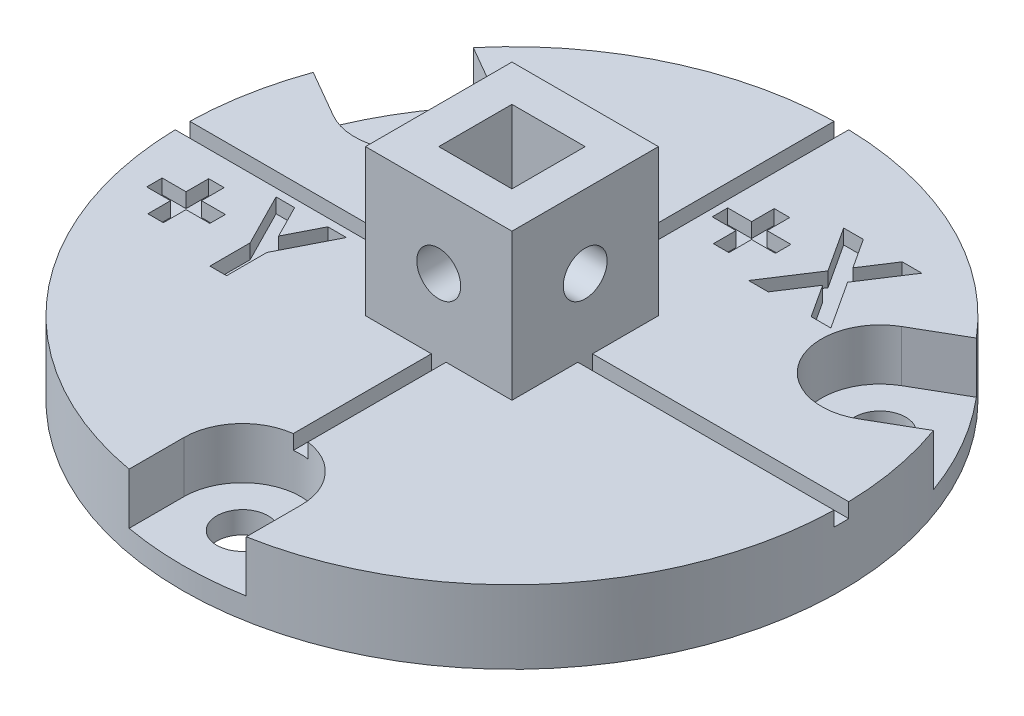
SolidWorks part; units mm, degrees
ref_plane "Front" through (0, 0, 0) normal (0, 0, 1) x (1, 0, 0)
ref_plane "Top" through (0, 0, 0) normal (0, 1, 0) x (1, 0, 0)
ref_plane "Right" through (0, 0, 0) normal (1, 0, 0) x (0, 0, -1)
sketch "Sketch1" plane through (0, 0, 0) normal (0, 1, 0) x (1, 0, 0)
  line L0 (0, 22.5) -> (0, -22.5) construction
  line L1 (22.5, 0) -> (-22.5, 0) construction
  circle A0 centre (0, 0) radius 22.5
  circle A1 centre (0, 0) radius 18.4 construction
  arc A2 (-10.9795, -19.6393) -> (-7.9114, -21.0632) centre (-9.4455, -20.3512) cw construction
  point P19 (0, 0)
  dimension "D1" = 45
  dimension "D2" = 36.8
extrude "plate" add sketch "Sketch1" along normal blind 5
sketch "Sketch6" plane through (0, 5, 0) normal (0, 1, 0) x (1, 0, 0)
  line L0 (0, 22.5) -> (0, -22.5) construction
  line L1 (0, -22.5) -> (0, -18.4) construction
  line L2 (-4, -22.5) -> (-4, -18.4)
  line L3 (4, -22.5) -> (4, -18.4)
  circle A1 centre (0, 0) radius 18.4 construction
  circle A2 centre (0, 0) radius 22.5 construction
  arc A3 (-4, -22.5) -> (4, -22.5) centre (0, -22.5) ccw
  arc A4 (4, -18.4) -> (-4, -18.4) centre (0, -18.4) ccw
  point P7 (0, -20.45)
  dimension "D1" = 4
extrude "opening for screw" cut sketch "Sketch6" against normal blind 5 from offset 1.5 contours L3 A4 L2 A3
sketch "Sketch7" plane through (0, 1.5, 0) normal (0, 1, 0) x (1, 0, 0)
  line L0 (0, 22.5) -> (0, -22.5) construction
  circle A0 centre (0, -18.4) radius 1.75
  circle A1 centre (0, 0) radius 18.4 construction
  dimension "D1" = 3.5
extrude "screw hole" cut sketch "Sketch7" against normal blind 5
pattern_circular "CirPattern20" count 3 over 360 about axis through (0, 0, 0) along (0, 1, 0) of "opening for screw", "screw hole"
sketch "Sketch10" plane through (0, 5, 0) normal (0, 1, 0) x (1, 0, 0)
  line L1 (-22.5, 0.5) -> (22.5, 0.5)
  line L2 (-22.5, 0.5) -> (-22.5, -0.5)
  line L3 (-22.5, -0.5) -> (22.5, -0.5)
  line L4 (22.5, 0.5) -> (22.5, -0.5)
  line L5 (-0.5, 22.5) -> (0.5, 22.5)
  line L6 (-0.5, 22.5) -> (-0.5, -22.5)
  line L7 (-0.5, -22.5) -> (0.5, -22.5)
  line L8 (0.5, 22.5) -> (0.5, -22.5)
  line L9 (0, 22.5) -> (0, -22.5) construction
  point P4 (22.5, 0)
  point P9 (-22.5, 0)
  point P14 (0, -22.5)
  point P15 (0, 22.5)
  dimension "D1" = 1
  dimension "D2" = 1
extrude "Cut-Extrude5" cut sketch "Sketch10" against normal blind 1 contours L6 L7 L8 L5 | L1 L4 L3 L2
sketch "Sketch11" plane through (0, 5, 0) normal (0, 1, 0) x (1, 0, 0)
  line L0 (0.5, 22.4944) -> (0.5, 0.5) construction
  text T0 "<b>+X</b>"
  text T1 "<b>+Y</b>"
extrude "Cut-Extrude6" cut sketch "Sketch11" against normal blind 1
sketch "Sketch12" plane through (0, 5, 0) normal (0, 1, 0) x (1, 0, 0)
  line L0 (0, 5) -> (0, -5) construction
  line L1 (-5, 5) -> (5, 5)
  line L2 (-5, 5) -> (-5, -5)
  line L3 (-5, -5) -> (5, -5)
  line L4 (5, 5) -> (5, -5)
  line L5 (-5, 0) -> (5, 0) construction
  line L9 (-2.5, 2.5) -> (2.5, 2.5)
  line L10 (-2.5, 2.5) -> (-2.5, -2.5)
  line L11 (-2.5, -2.5) -> (2.5, -2.5)
  line L12 (2.5, 2.5) -> (2.5, -2.5)
  point P8 (0, 0)
  point P9 (0, 0)
  dimension "D1" = 10
  dimension "D2" = 5
extrude "tool connect piece" add sketch "Sketch12" along normal blind 10 and the other way up to surface (1 mm away) contours L9 L12 L11 L10 | L4 L3 L2 L1
sketch "Sketch14" plane through (0, 0, -5) normal (0, 0, -1) x (-1, 0, 0)
  line L0 (-5, 10) -> (5, 10) construction
  line L1 (-5, 5) -> (-5, 15) construction
  line L2 (5, 5) -> (5, 15) construction
  circle A0 centre (0, 10) radius 1.5
  point P8 (0, 11.0324)
  point P9 (0, 0)
  dimension "D1" = 3
extrude "Cut-Extrude8" cut sketch "Sketch14" against normal blind 10 contours A0
sketch "Sketch15" plane through (5, 0, 0) normal (1, 0, 0) x (0, 0, -1)
  line L0 (5, 10) -> (-5, 10) construction
  line L1 (5, 5) -> (5, 15) construction
  line L2 (-5, 5) -> (-5, 15) construction
  circle A0 centre (0, 10) radius 1.5
  dimension "D1" = 3
extrude "Cut-Extrude9" cut sketch "Sketch15" against normal through all
